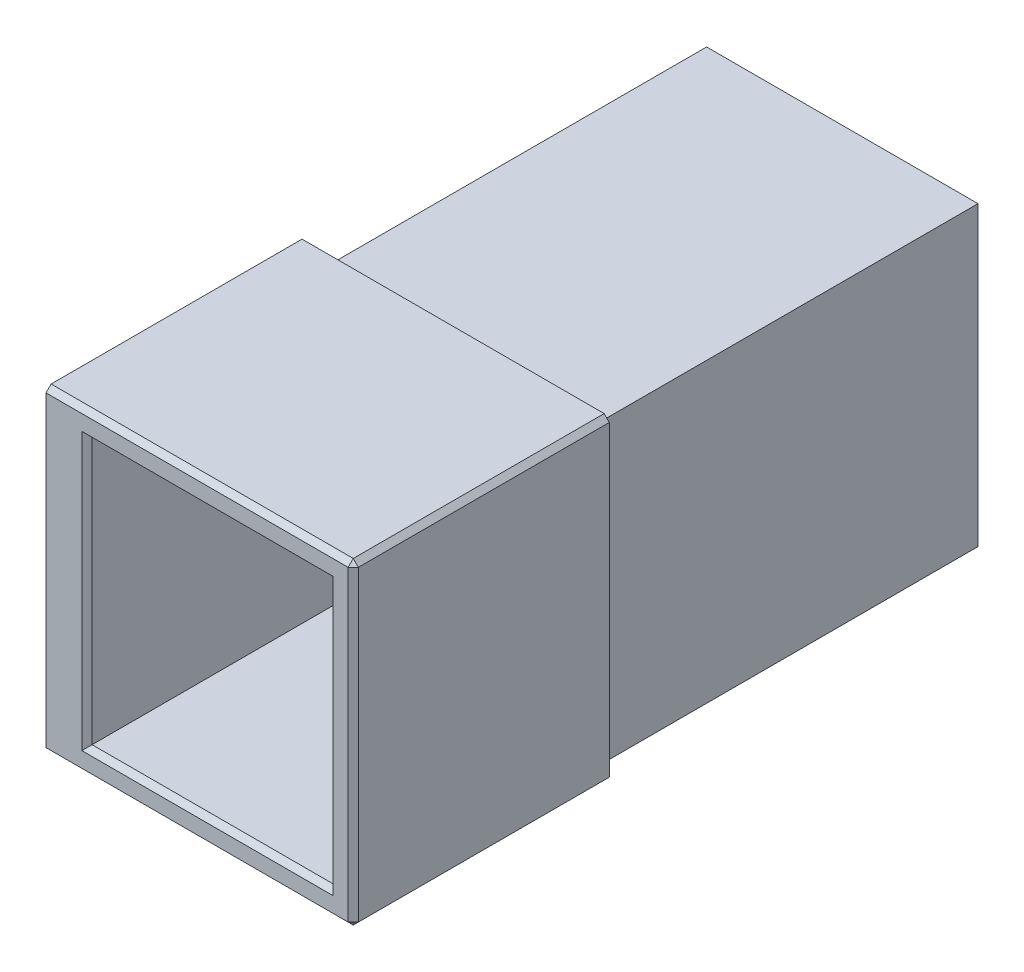
SolidWorks part; units mm, degrees
material "Petg 30% Infill"
ref_plane "Front Plane" through (0, 0, 0) normal (0, 0, 1) x (1, 0, 0)
ref_plane "Top Plane" through (0, 0, 0) normal (0, 1, 0) x (1, 0, 0)
ref_plane "Right Plane" through (0, 0, 0) normal (1, 0, 0) x (0, 0, -1)
sketch "Sketch1" plane through (0, 0, 0) normal (0, 0, 1) x (1, 0, 0)
  line L0 (17.5408, -97.5447) -> (17.5408, -113.5447)
  line L5 (64.5408, -92.5447) -> (17.5408, -92.5447)
  line L6 (64.5408, -92.5447) -> (64.5408, -40.5447)
  line L7 (64.5408, -40.5447) -> (17.5408, -40.5447)
  line L8 (17.5408, -92.5447) -> (17.5408, -40.5447)
  line L9 (64.5408, -92.5447) -> (17.5408, -40.5447) construction
  line L10 (64.5408, -40.5447) -> (17.5408, -92.5447) construction
  line L11 (69.5408, -97.5447) -> (17.5408, -97.5447)
  line L12 (69.5408, -97.5447) -> (69.5408, -35.5447)
  line L13 (69.5408, -35.5447) -> (9.5408, -35.5447)
  line L14 (9.5408, -113.5447) -> (9.5408, -35.5447)
  line L17 (17.5408, -113.5447) -> (9.5408, -113.5447)
  point P5 (41.0408, -66.5447)
  point P10 (41.0408, -66.5447)
  dimension "D1" = 8
  dimension "D2" = 47
  dimension "D3" = 52
  dimension "D5" = 78
  dimension "D6" = 5
  dimension "D4" = 5
  dimension "D7" = 5
extrude "Boss-Extrude1" add sketch "Sketch1" along normal blind 50
sketch "Sketch8" plane through (17.5408, 0, 0) normal (1, 0, 0) x (0, 0, -1)
  line L0 (-50, -97.5447) -> (0, -97.5447) construction
  line L1 (-50, -113.5447) -> (-25, -113.5447)
  line L2 (-50, -113.5447) -> (-50, -97.5447)
  line L3 (-50, -97.5447) -> (-25, -97.5447)
  line L4 (-25, -113.5447) -> (-25, -97.5447)
extrude "Cut-Extrude1" cut sketch "Sketch8" against normal blind 10
sketch "Sketch9" plane through (9.5408, 0, 0) normal (-1, 0, 0) x (0, 0, 1)
  line L0 (35, -46.0447) -> (28, -46.0447) construction
  line L1 (35, -49.7947) -> (28, -49.7947)
  line L2 (35, -42.2947) -> (28, -42.2947)
  line L3 (15, -103.0447) -> (8, -103.0447) construction
  line L4 (15, -106.7947) -> (8, -106.7947)
  line L5 (15, -99.2947) -> (8, -99.2947)
  line L6 (25, -113.5447) -> (25, -97.5447) construction
  line L7 (0, -74.5447) -> (21.5, -74.5447) construction
  line L8 (0, -35.5447) -> (0, -113.5447) construction
  line L9 (31.5, -46.0447) -> (11.5, -103.0447) construction
  arc A0 (35, -49.7947) -> (35, -42.2947) centre (35, -46.0447) ccw
  arc A1 (28, -42.2947) -> (28, -49.7947) centre (28, -46.0447) ccw
  arc A2 (15, -106.7947) -> (15, -99.2947) centre (15, -103.0447) ccw
  arc A3 (8, -99.2947) -> (8, -106.7947) centre (8, -103.0447) ccw
  point P2 (31.5, -46.0447)
  point P7 (11.5, -103.0447)
  point P22 (21.5, -74.5447)
  point P23 (21.5, -74.5447)
  dimension "D1" = 7.5
  dimension "D2" = 10
  dimension "D3" = 10
  dimension "D4" = 7
  dimension "D5" = 57
extrude "Cut-Extrude2" cut sketch "Sketch9" against normal blind 3.5 from offset 2 offset against normal yes
sketch "Sketch10" plane through (9.5408, 0, 0) normal (-1, 0, 0) x (0, 0, 1)
  line L0 (35, -46.0447) -> (28, -46.0447) construction
  line L1 (35, -48.0947) -> (32.4788, -48.0947)
  line L2 (35, -43.9947) -> (32.4788, -43.9947)
  line L3 (8, -103.0447) -> (15, -103.0447) construction
  line L4 (12.4788, -100.9947) -> (15, -100.9947)
  line L5 (12.4788, -105.0947) -> (15, -105.0947)
  arc A0 (30.4882, -43.2391) -> (30.4882, -48.8502) centre (28, -46.0447) ccw
  arc A1 (10.4882, -100.2391) -> (10.4882, -105.8502) centre (8, -103.0447) ccw
  arc A2 (35, -48.0947) -> (35, -43.9947) centre (35, -46.0447) ccw
  arc A5 (15, -105.0947) -> (15, -100.9947) centre (15, -103.0447) ccw
  arc A6 (8, -99.2947) -> (8, -106.7947) centre (8, -103.0447) ccw construction
  arc A7 (15, -106.7947) -> (15, -99.2947) centre (15, -103.0447) ccw construction
  arc A8 (28, -42.2947) -> (28, -49.7947) centre (28, -46.0447) ccw construction
  arc A9 (35, -49.7947) -> (35, -42.2947) centre (35, -46.0447) ccw construction
  arc A10 (30.4882, -43.2391) -> (32.4788, -43.9947) centre (32.4788, -40.9947) ccw
  arc A11 (32.4788, -48.0947) -> (30.4882, -48.8502) centre (32.4788, -51.0947) ccw
  arc A12 (10.4882, -100.2391) -> (12.4788, -100.9947) centre (12.4788, -97.9947) ccw
  arc A13 (12.4788, -105.0947) -> (10.4882, -105.8502) centre (12.4788, -108.0947) ccw
  point P5 (31.9062, -46.5675)
  point P10 (11.5, -103.0447)
  point P17 (0, 0)
  point P21 (0, 0)
  point P25 (0, 0)
  point P30 (15, -103.0447)
  point P31 (0, 0)
  point P32 (16.276, -100.6973)
  dimension "D3" = 3
  dimension "D1" = 4.1
  dimension "D2" = 4.1
extrude "Cut-Extrude3" cut sketch "Sketch10" against normal blind 3.5
chamfer "Chamfer1" distance 1 angle 45 13 edges at (17.5408, -66.5447, 50) (41.0408, -92.5447, 50) (41.0408, -40.5447, 50) (64.5408, -66.5447, 50) (17.5408, -113.5447, 12.5) (39.5408, -97.5447, 50) (39.5408, -35.5447, 50) (69.5408, -97.5447, 25) (69.5408, -66.5447, 50) (69.5408, -35.5447, 25) (17.5408, -97.5447, 12.5) (13.5408, -97.5447, 25) (17.5408, -105.5447, 25)
sketch "Sketch6" plane through (0, 0, 0) normal (0, 0, -1) x (-1, 0, 0)
  line L0 (-64.5408, -40.5447) -> (-17.5408, -40.5447) construction
  line L1 (-64.5408, -92.5447) -> (-64.5408, -40.5447) construction
  line L2 (-17.5408, -40.5447) -> (-17.5408, -92.5447) construction
  line L3 (-17.5408, -92.5447) -> (-64.5408, -92.5447) construction
  line L4 (-64.5408, -40.5447) -> (-17.5408, -40.5447)
  line L5 (-64.5408, -92.5447) -> (-64.5408, -40.5447)
  line L6 (-17.5408, -40.5447) -> (-17.5408, -92.5447)
  line L7 (-17.5408, -92.5447) -> (-64.5408, -92.5447)
  line L8 (-67.5408, -37.5447) -> (-14.5408, -37.5447)
  line L9 (-14.5408, -37.5447) -> (-14.5408, -95.5447)
  line L10 (-14.5408, -95.5447) -> (-67.5408, -95.5447)
  line L11 (-67.5408, -95.5447) -> (-67.5408, -37.5447)
  dimension "D1" = 3
extrude "Boss-Extrude3" add sketch "Sketch6" along normal blind 74
chamfer "Chamfer2" distance 1 angle 45 4 edges at (41.0408, -95.5447, 0) (14.5408, -66.5447, 0) (41.0408, -37.5447, 0) (67.5408, -66.5447, 0)
equation "\"D4@Sketch1\"=\"D6@Sketch1\""
equation "\"D7@Sketch1\"=\"D6@Sketch1\""
